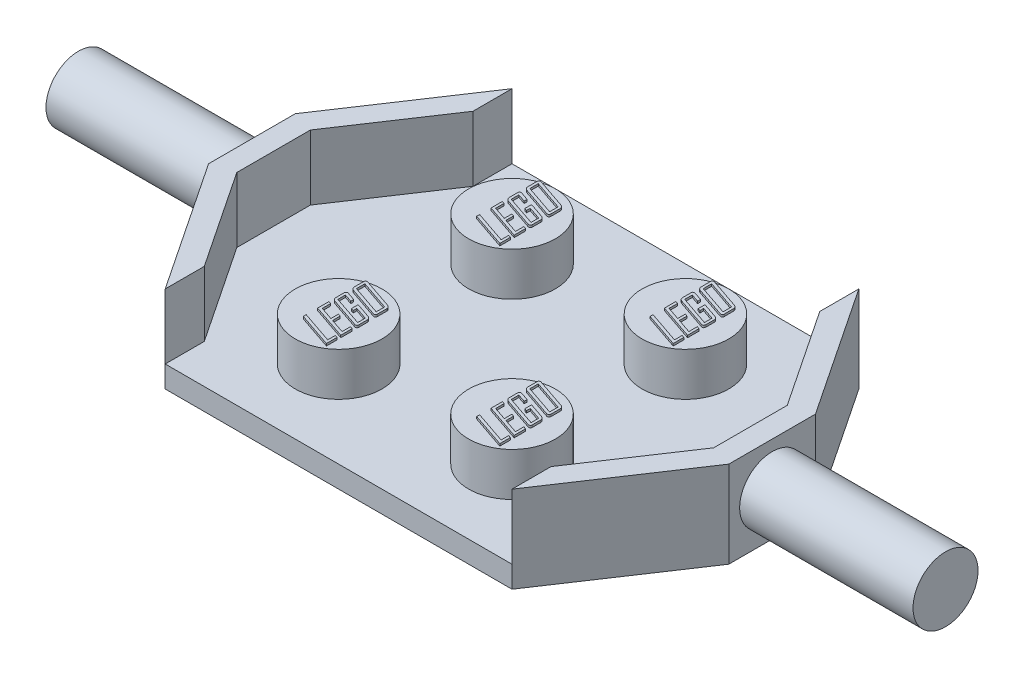
SolidWorks part; units mm, degrees
material "ABS"
ref_plane "Front Plane" through (0, 0, 0) normal (0, 0, 1) x (1, 0, 0)
ref_plane "Top Plane" through (0, 0, 0) normal (0, 1, 0) x (1, 0, 0)
ref_plane "Right Plane" through (0, 0, 0) normal (1, 0, 0) x (0, 0, -1)
sketch "Sketch1" plane through (0, 0, 0) normal (0, 1, 0) x (1, 0, 0)
  line L0 (0, 0) -> (-12, 0) construction
  line L1 (-12, -2) -> (-12, 2)
  line L2 (-12, 2) -> (-8, 8)
  line L3 (-8, 8) -> (0, 8)
  line L4 (0, 8) -> (0, -8)
  line L5 (-8, -8) -> (0, -8)
  line L6 (-12, -2) -> (-8, -8)
  dimension "D1" = 12
  dimension "D2" = 2
  dimension "D3" = 8
  dimension "D4" = 8
extrude "Boss-Extrude1" add sketch "Sketch1" along normal blind 1
sketch "Sketch2" plane through (0, 1, 0) normal (0, 1, 0) x (1, 0, 0)
  line L0 (0, 0) -> (-12, 0) construction
  line L1 (-12, 2) -> (-12, -2) construction
  line L2 (0, -8) -> (0, 8) construction
  line L3 (0, 8) -> (-8, 8) construction
  circle A0 centre (-4, 4) radius 2
  circle A1 centre (-4, -4) radius 2
  dimension "D1" = 4
  dimension "D2" = 4
  dimension "D3" = 4
extrude "Boss-Extrude2" add sketch "Sketch2" along normal blind 2
sketch "Sketch3" plane through (0, 1, 0) normal (0, 1, 0) x (1, 0, 0)
  line L0 (-12, -2) -> (-8, -8) construction
  line L1 (-12, 2) -> (-12, -2) construction
  line L2 (-8, 8) -> (-12, 2) construction
  line L3 (-12, -2) -> (-8, -8)
  line L4 (-12, 2) -> (-12, -2)
  line L5 (-8, 8) -> (-12, 2)
  line L6 (-8, 6.1972) -> (-11, 1.6972)
  line L7 (-11, 1.6972) -> (-11, -1.6972)
  line L8 (-11, -1.6972) -> (-8, -6.1972)
  line L9 (-8, 8) -> (-8, 6.1972)
  line L10 (-7.1679, 7.4453) -> (-11, 1.6972) construction
  line L11 (-8, -6.1972) -> (-8, -8)
  line L12 (-11, -1.6972) -> (-7.1679, -7.4453) construction
  dimension "D1" = 1
extrude "Boss-Extrude3" add sketch "Sketch3" along normal blind 3
sketch "Sketch4" plane through (-12, 0, 0) normal (-1, 0, 0) x (0, 0, 1)
  line L0 (0, 0) -> (0, 4) construction
  line L1 (-2, 0) -> (2, 0) construction
  line L2 (-2, 4) -> (2, 4) construction
  circle A0 centre (0, 2) radius 1.5
  dimension "D1" = 3
extrude "Boss-Extrude4" add sketch "Sketch4" along normal blind 8
mirror "Mirror1" about plane through (0, 0, 0) normal (1, 0, 0) of bodies 104
sketch "Sketch5" plane through (0, 3, 0) normal (0, 1, 0) x (1, 0, 0)
  line L0 (-4, -6) -> (-4, -2) construction
  line L1 (-4, -2) -> (-3, -2) construction
  line L2 (-3, -2) -> (-3, -5.7) construction
  circle A0 centre (-4, -4) radius 2 construction
  circle A1 centre (-4, -4) radius 2 construction
  text T0 "<i>LEGO</i>" font "Agency FB" height in points 6
  dimension "D1" = 1
  dimension "D2" = 3.7
extrude "Boss-Extrude5" add sketch "Sketch5" along normal blind 0.1
pattern_linear "LPattern1" count 2 spacing 8 along (0, 0, -1) count 2 spacing 8 of "Boss-Extrude5"
